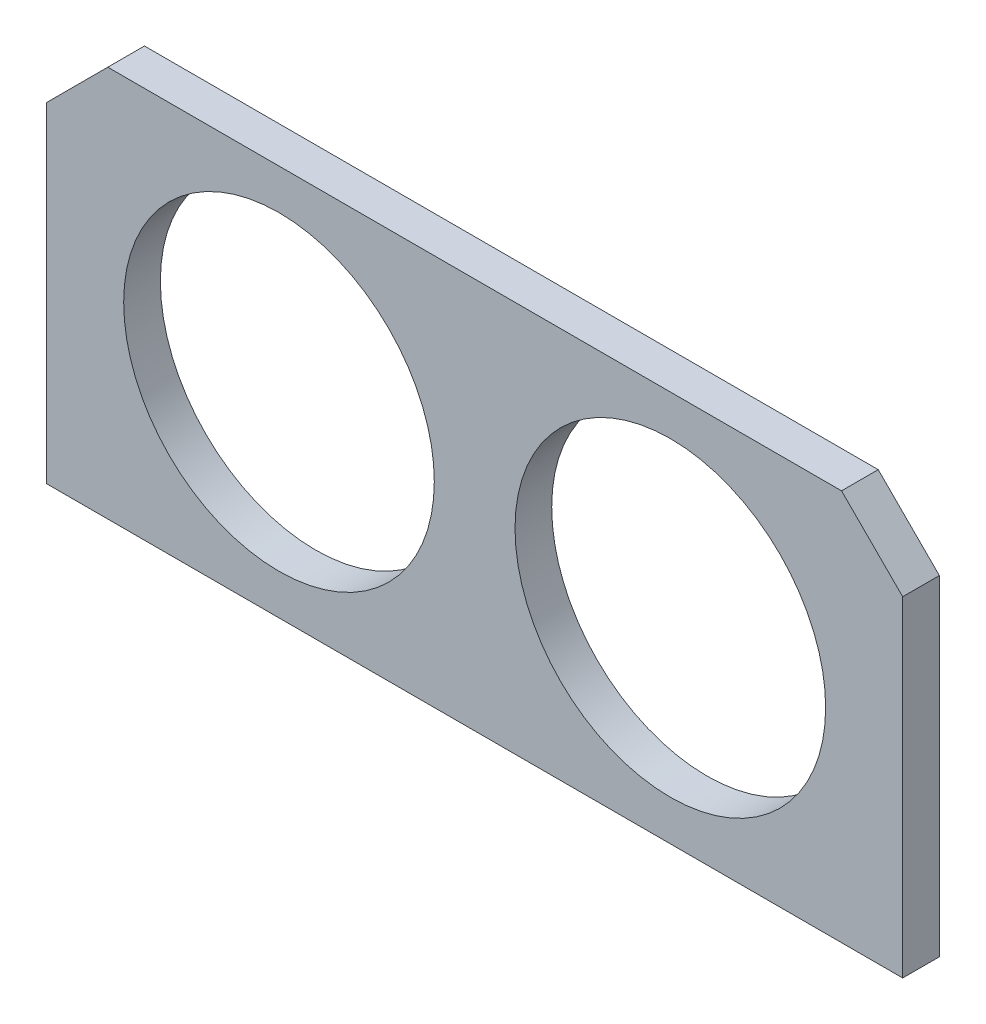
SolidWorks part; units mm, degrees
ref_plane "Front Plane" through (0, 0, 0) normal (0, 0, 1) x (1, 0, 0)
ref_plane "Top Plane" through (0, 0, 0) normal (0, 1, 0) x (1, 0, 0)
ref_plane "Right Plane" through (0, 0, 0) normal (1, 0, 0) x (0, 0, -1)
sketch "Sketch1" plane through (0, 0, 0) normal (0, 0, 1) x (1, 0, 0)
  line L0 (-59.698, 24.8446) -> (-78.698, 24.8446) construction
  line L2 (-78.698, 24.8446) -> (-78.698, 40.8446)
  line L3 (-78.698, 24.8446) -> (-78.698, 8.8446)
  line L4 (-59.698, 24.8446) -> (-59.698, 8.8446) construction
  line L5 (-59.698, 8.8446) -> (-78.698, 8.8446)
  line L6 (-59.698, 8.8446) -> (-8.698, 8.8446)
  line L7 (-27.698, 24.8446) -> (-27.698, 8.8446) construction
  line L8 (-59.698, 24.8446) -> (-59.698, 40.8446) construction
  line L9 (-59.698, 40.8446) -> (-8.698, 40.8446)
  line L10 (-27.698, 24.8446) -> (-27.698, 40.8446) construction
  line L11 (-59.698, 40.8446) -> (-78.698, 40.8446)
  line L12 (-27.698, 24.8446) -> (-8.698, 24.8446) construction
  line L14 (-8.698, 40.8446) -> (-8.698, 8.8446)
  circle A0 centre (-59.698, 24.8446) radius 12.7
  circle A1 centre (-27.698, 24.8446) radius 12.7
  dimension "D3" = 25.4
  dimension "D1" = 16
extrude "Boss-Extrude1" add sketch "Sketch1" along normal blind 3 contours A0 | A1 | L9 L14 L6 L5 L3 L2 L11
chamfer "Chamfer1" distance 5 angle 45 2 edges at (-8.698, 40.8446, 1.5) (-78.698, 40.8446, 1.5)
